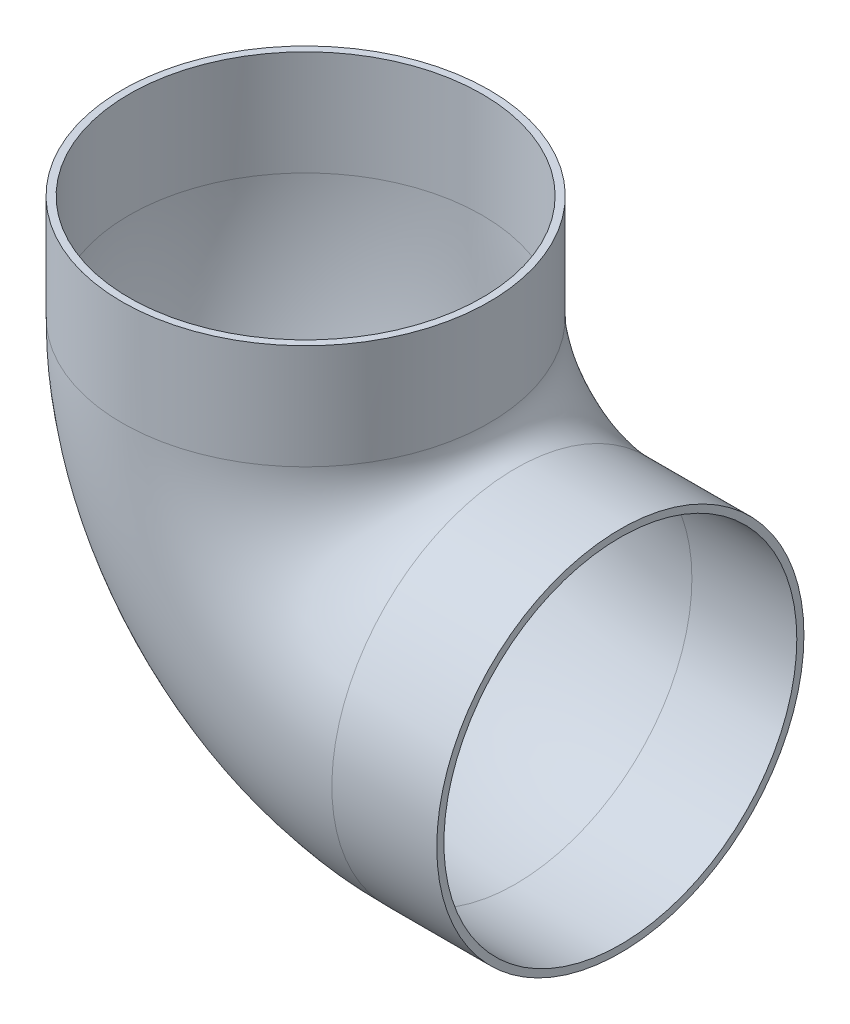
SolidWorks part; units mm, degrees
material "PVC 0.007 Plasticized"
ref_plane "Front Plane" through (0, 0, 0) normal (0, 0, 1) x (1, 0, 0)
ref_plane "Top Plane" through (0, 0, 0) normal (0, 1, 0) x (1, 0, 0)
ref_plane "Right Plane" through (0, 0, 0) normal (1, 0, 0) x (0, 0, -1)
sketch "Sketch1" plane through (0, 0, 0) normal (0, 0, 1) x (1, 0, 0)
  line L0 (-18.2819, 1.9178) -> (-18.2819, -4.4322)
  line L1 (-5.5819, -17.1322) -> (0.7681, -17.1322)
  arc A0 (-18.2819, -4.4322) -> (-5.5819, -17.1322) centre (-5.5819, -4.4322) ccw
  point P4 (0, 0)
  dimension "D1" = 12.7
  dimension "D2" = 19.05
  dimension "D3" = 12.7
  dimension "D4" = 19.05
ref_plane "Plane1" through (0.7681, -17.1322, 0) normal (1, 0, 0) x (0, 0, -1)
sketch "Sketch2" plane through (0.7681, -17.1322, 0) normal (1, 0, 0) x (0, 0, -1)
  circle A0 centre (0, 0) radius 11.1125
  circle A1 centre (0, 0) radius 10.6807
  dimension "D1" = 22.225
  dimension "D2" = 21.3614
sweep "Sweep1" add profiles "Sketch2" path "Sketch1"
sketch "Sketch3" plane through (0.7681, -17.1322, 0) normal (1, 0, 0) x (0, 0, -1)
  circle A0 centre (0, 0) radius 10.6934
  circle A1 centre (0, 0) radius 10.6807 construction
  point P2 (0, 0)
  dimension "D1" = 21.3868
extrude "Cut-Extrude1" [suppressed] cut sketch "Sketch3" against normal blind 6.35
